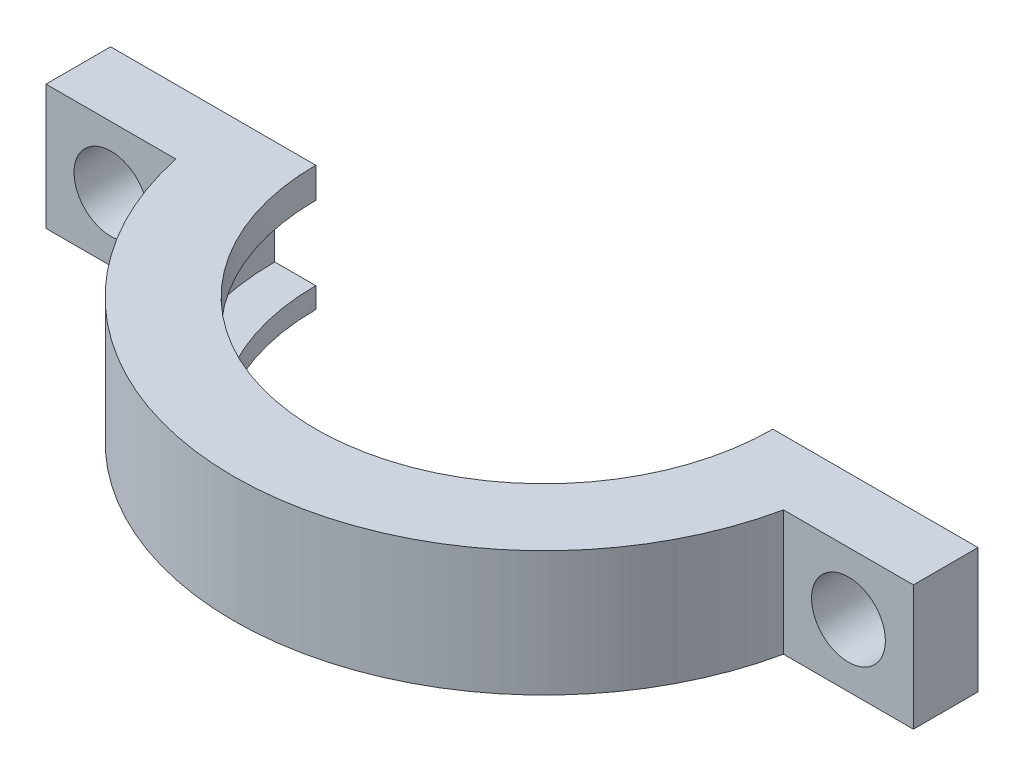
SolidWorks part; units mm, degrees
ref_plane "Front Plane" through (0, 0, 0) normal (0, 0, 1) x (1, 0, 0)
ref_plane "Top Plane" through (0, 0, 0) normal (0, 1, 0) x (1, 0, 0)
ref_plane "Right Plane" through (0, 0, 0) normal (1, 0, 0) x (0, 0, -1)
sketch "Sketch3" plane through (0, 0, 0) normal (0, 0, 1) x (1, 0, 0)
  line L2 (-62.6943, 11.7337) -> (-64.8845, 11.7337)
  line L3 (-62.8845, 10.2507) -> (-60.8845, 10.2507)
  line L5 (-60.8845, 6.6507) -> (-62.8845, 6.6507)
  line L6 (-62.8845, 6.6507) -> (-62.8845, 10.2507)
  line L10 (-64.8845, 11.7337) -> (-64.8845, 5.6398)
  line L11 (-64.8845, 5.6398) -> (-60.8845, 5.6398)
  line L12 (-60.8845, 5.6398) -> (-60.8845, 6.6507)
  line L13 (-60.8845, 10.2507) -> (-60.8845, 11.7337)
  line L14 (-60.8845, 11.7337) -> (-62.6943, 11.7337)
  dimension "D2" = 2
  dimension "D3" = 4
  dimension "D1" = 2
  dimension "D4" = 3.6
sketch "Sketch4" plane through (0, 0, 0) normal (0, 0, 1) x (1, 0, 0)
  line L0 (-49.7443, 0) -> (-49.7443, 12.8648) construction
  line L1 (27.6543, 0) -> (-27.6543, 0) construction
revolve "Revolve1" add sketch "Sketch3" angle 360 about L0
sketch "Sketch7" plane through (0, 11.7337, 0) normal (0, 1, 0) x (1, 0, 0)
  line L2 (-50.2443, 15.132) -> (-50.2443, 13.1308)
  line L3 (-49.2443, 15.132) -> (-49.2443, 13.1308)
  circle A0 centre (-49.7443, 0) radius 15.1403 construction
  arc A1 (-49.2443, 15.132) -> (-50.2443, 15.132) centre (-49.7443, 0) ccw
  circle A2 centre (-49.7443, 0) radius 13.1403 construction
  arc A3 (-49.2443, 13.1308) -> (-50.2443, 13.1308) centre (-49.7443, 0) ccw
  point P9 (-49.7443, 14.131)
  dimension "D1" = 1
extrude "Boss-Extrude1" add sketch "Sketch7" along normal blind 5
sketch "Sketch8" plane through (0, 16.7337, 0) normal (0, 1, 0) x (1, 0, 0)
  line L0 (-50.2443, 15.132) -> (-50.2443, 13.1308) construction
  line L3 (-50.2443, 15.132) -> (-50.2443, 13.1308)
  line L4 (-49.2443, 13.1308) -> (-49.2443, 15.132) construction
  line L5 (-49.2443, 13.1308) -> (-49.2443, 15.132)
  line L6 (-50.2443, 13.1308) -> (-50.2443, -4.3692)
  line L7 (-50.2443, -4.3692) -> (-49.2443, -4.3692)
  line L8 (-49.2443, -4.3692) -> (-49.2443, 13.1308)
  arc A0 (-49.2443, 15.132) -> (-50.2443, 15.132) centre (-49.7443, 0) ccw construction
  arc A1 (-49.2443, 15.132) -> (-50.2443, 15.132) centre (-49.7443, 0) ccw
  dimension "D1" = 17.5
extrude "Boss-Extrude2" add sketch "Sketch8" against normal blind 3
sketch "Sketch9" plane through (0, 11.7337, 0) normal (0, 1, 0) x (1, 0, 0)
  line L2 (-54.4943, 14.3759) -> (-54.4943, 39.3759)
  line L3 (-54.4943, 39.3759) -> (-44.9943, 39.3759)
  line L4 (-44.9943, 39.3759) -> (-44.9943, 14.3759)
  arc A0 (-50.2443, 15.132) -> (-49.2443, 15.132) centre (-49.7443, 0) ccw construction
  arc A1 (-50.2443, 15.132) -> (-54.4943, 14.3759) centre (-49.7443, 0) ccw
  arc A2 (-49.2443, 15.132) -> (-50.2443, 15.132) centre (-49.7443, 0) ccw construction
  arc A3 (-49.2443, 15.132) -> (-50.2443, 15.132) centre (-49.7443, 0) ccw
  arc A4 (-44.9943, 14.3759) -> (-49.2443, 15.132) centre (-49.7443, 0) ccw
  point P9 (-49.7443, 0)
  dimension "D1" = 25
extrude "Boss-Extrude3" add sketch "Sketch9" against normal blind 3
sketch "Sketch10" plane through (0, 8.7337, 0) normal (0, -1, 0) x (1, 0, 0)
  line L0 (-44.9943, -14.3759) -> (-44.9943, -39.3759) construction
  line L1 (-54.4943, -39.3759) -> (-44.9943, -39.3759)
  line L2 (-54.4943, -39.3759) -> (-54.4943, -34.3759)
  line L3 (-54.4943, -34.3759) -> (-44.9943, -34.3759)
  line L4 (-44.9943, -39.3759) -> (-44.9943, -34.3759)
  dimension "D1" = 5
extrude "Boss-Extrude4" add sketch "Sketch10" along normal blind 15.78
sketch "Sketch11" plane through (0, 0, -39.3759) normal (0, 0, -1) x (-1, 0, 0)
  line L0 (54.4943, -7.0463) -> (54.4943, 11.7337) construction
  line L1 (44.9943, -7.0463) -> (54.4943, -7.0463)
  line L2 (44.9943, -7.0463) -> (44.9943, -5.0463)
  line L3 (44.9943, -5.0463) -> (54.4943, -5.0463)
  line L4 (54.4943, -7.0463) -> (54.4943, -5.0463)
  dimension "D1" = 2
extrude "Boss-Extrude5" add sketch "Sketch11" along normal blind 40
sketch "Sketch13" plane through (0, 11.7337, 0) normal (0, 1, 0) x (1, 0, 0)
  line L2 (-49.7443, 3.15) -> (-49.7443, -3.15) construction
  line L3 (-28.604, 3.15) -> (-34.9353, 3.15)
  line L4 (-70.8845, 3.15) -> (-70.8845, -3.15)
  line L5 (-70.8845, -3.15) -> (-64.5532, -3.15)
  line L6 (-28.604, -3.15) -> (-28.604, 3.15)
  line L7 (-64.5532, 3.15) -> (-70.8845, 3.15)
  line L8 (-34.9353, -3.15) -> (-28.604, -3.15)
  arc A0 (-54.4943, 14.3759) -> (-44.9943, 14.3759) centre (-49.7443, 0) ccw construction
  arc A1 (-64.5532, 3.15) -> (-64.5532, -3.15) centre (-49.7443, 0) ccw
  arc A2 (-34.9353, -3.15) -> (-34.9353, 3.15) centre (-49.7443, 0) ccw
  point P10 (-49.7443, 0)
  point P13 (-49.7443, 3.15)
  dimension "D1" = 6.3
extrude "Boss-Extrude6" add sketch "Sketch13" against normal up to surface (6.0939 mm away) up to face at (-49.7443, 5.6398, -11.1403)
sketch "Sketch14" plane through (0, 0, 3.15) normal (0, 0, 1) x (1, 0, 0)
  line L0 (-70.8845, 11.7337) -> (-64.5532, 5.6398) construction
  line L1 (-28.604, 11.7337) -> (-34.9353, 5.6398) construction
  circle A0 centre (-31.7697, 8.6868) radius 1.8
  circle A1 centre (-67.7189, 8.6868) radius 1.8
  dimension "D1" = 3.6
  dimension "D2" = 3.6
extrude "Cut-Extrude1" cut sketch "Sketch14" against normal up to surface (6.3 mm away) contours A1 | A0 up to face at (-67.7189, 8.6868, -3.15)
sketch "Sketch15" plane through (0, 11.7337, 0) normal (0, 1, 0) x (1, 0, 0)
  line L0 (-70.8845, 0) -> (-23.4421, 0) construction
  line L1 (-70.8845, 3.15) -> (-70.8845, -3.15) construction
  line L2 (-55, 0) -> (55, 0) construction
  line L4 (-23.4421, 0) -> (-74.5953, 0)
  line L5 (-23.4421, 0) -> (-23.4421, 86.0506)
  line L6 (-23.4421, 86.0506) -> (-74.5953, 86.0506)
  line L7 (-74.5953, 0) -> (-74.5953, 86.0506)
extrude "Cut-Extrude3" cut sketch "Sketch15" against normal through all both and the other way through all
sketch "Sketch16" plane through (0, 0, 0) normal (0, 1, 0) x (1, 0, 0)
  line L1 (-54.8883, 5.4174) -> (-45.2843, 5.4174)
  line L2 (-54.8883, 5.4174) -> (-54.8883, -6.4675)
  line L3 (-54.8883, -6.4675) -> (-45.2843, -6.4675)
  line L4 (-45.2843, 5.4174) -> (-45.2843, -6.4675)
extrude "Cut-Extrude4" cut sketch "Sketch16" along normal through all
